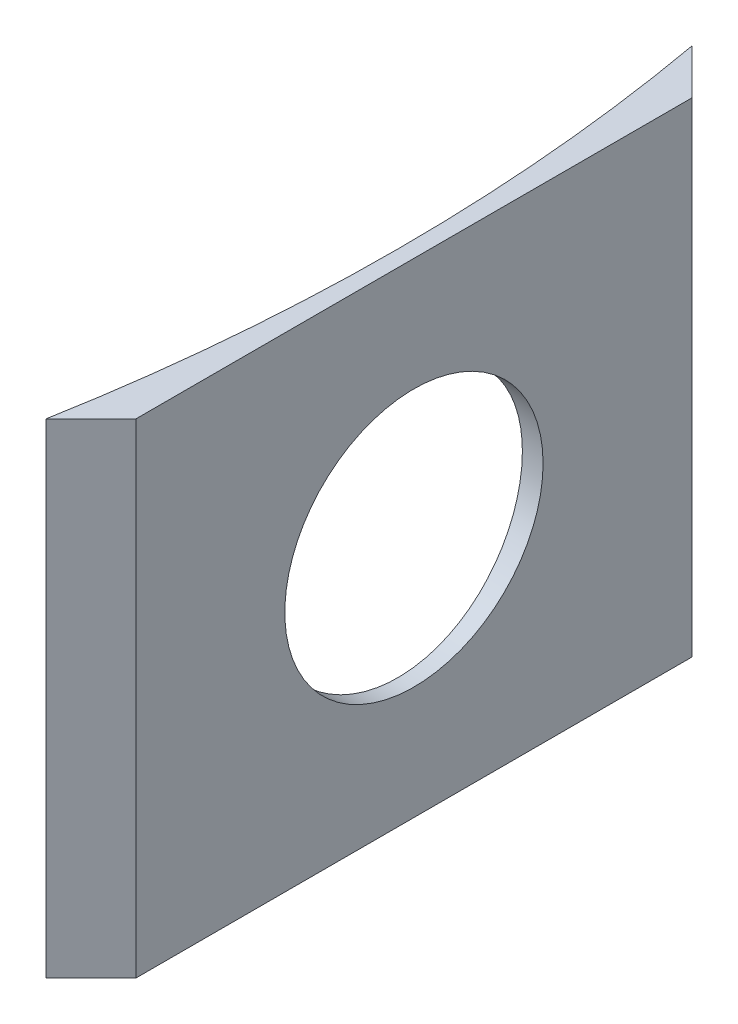
SolidWorks part; units mm, degrees
ref_plane "Front Plane" through (0, 0, 0) normal (0, 0, 1) x (1, 0, 0)
ref_plane "Top Plane" through (0, 0, 0) normal (0, 1, 0) x (1, 0, 0)
ref_plane "Right Plane" through (0, 0, 0) normal (1, 0, 0) x (0, 0, -1)
sketch "Sketch1" plane through (0, 0, 0) normal (0, 1, 0) x (1, 0, 0)
  line L0 (0, 0) -> (56.5, 0)
  line L1 (-0.6707, -0.0071) -> (55.608, 10)
  line L2 (-0.6707, -0.0071) -> (55.608, -10)
  line L3 (55.608, 10) -> (55.608, -10)
  line L4 (55.608, 10) -> (57, 8.608)
  line L5 (57, 8.608) -> (57, -8.608)
  line L6 (57, -8.608) -> (55.608, -10)
  circle A0 centre (0, 0) radius 56.5
  dimension "D1" = 113
  dimension "D2" = 90
  dimension "D3" = 20
  dimension "D4" = 135
  dimension "D5" = 135
  dimension "D6" = 0.5
extrude "Boss-Extrude1" add sketch "Sketch1" along normal blind 15 contours A0 L6 L5 L4
ref_plane "Plane1" through (67, 0, 0) normal (1, 0, 0) x (0, 0, -1)
sketch "Sketch2" plane through (67, 0, 0) normal (1, 0, 0) x (0, 0, -1)
  line L0 (0, 0) -> (0, 15)
  line L1 (8.608, 15) -> (-8.608, 15) construction
  circle A0 centre (0, 7.5) radius 4
  dimension "D1" = 8
extrude "Cut-Extrude1" cut sketch "Sketch2" against normal blind 25 contours L0 A0 | L0 A0
